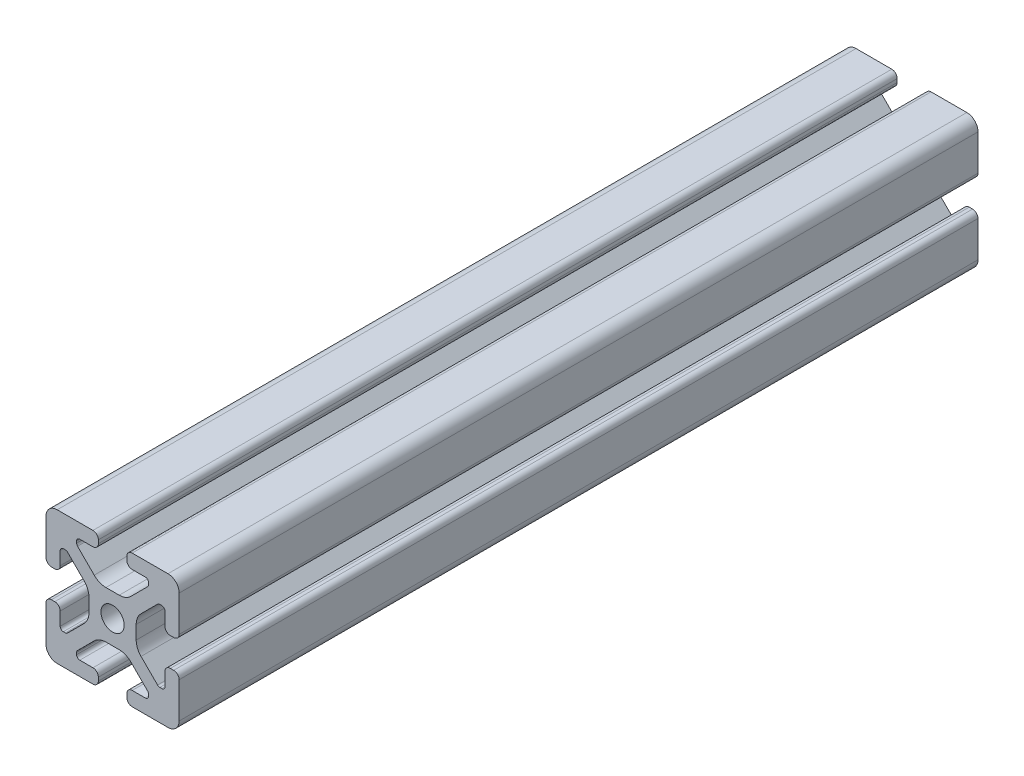
SolidWorks part; units mm, degrees
ref_plane "Front Plane" through (0, 0, 0) normal (0, 0, 1) x (1, 0, 0)
ref_plane "Top Plane" through (0, 0, 0) normal (0, 1, 0) x (1, 0, 0)
ref_plane "Right Plane" through (0, 0, 0) normal (1, 0, 0) x (0, 0, -1)
sketch "Sketch1" plane through (0, 0, 0) normal (0, 0, 1) x (1, 0, 0)
  point P0 (0, 0)
  line B0 (-4.064, 16.5396) -> (-4.064, 17.4964)
  line B1 (-5.6176, 19.05) -> (-15.8475, 19.05)
  line B2 (-19.05, 15.8475) -> (-19.05, 5.6176)
  line B3 (-17.4964, 4.064) -> (-16.5396, 4.064)
  line B4 (-14.986, 5.6176) -> (-14.986, 9.3853)
  line B5 (-14.0843, 10.287) -> (-13.516, 10.287)
  line B6 (-12.8784, 10.0229) -> (-8.1476, 5.2921)
  line B7 (-6.7564, 1.9335) -> (-6.7564, -1.9335)
  line B8 (-8.1476, -5.2921) -> (-12.8784, -10.0229)
  line B9 (-13.516, -10.287) -> (-14.0843, -10.287)
  line B10 (-14.986, -9.3853) -> (-14.986, -5.6176)
  line B11 (-16.5396, -4.064) -> (-17.4964, -4.064)
  line B12 (-19.05, -5.6176) -> (-19.05, -15.8475)
  line B13 (-15.8475, -19.05) -> (-5.6176, -19.05)
  line B14 (-4.064, -17.4964) -> (-4.064, -16.5396)
  line B15 (-5.6176, -14.986) -> (-9.3853, -14.986)
  line B16 (-10.287, -14.0843) -> (-10.287, -13.5524)
  line B17 (-10.0229, -12.9148) -> (-5.2522, -8.144)
  line B18 (-1.9022, -6.7564) -> (1.9022, -6.7564)
  line B19 (5.2522, -8.144) -> (10.0229, -12.9148)
  line B20 (10.287, -13.5524) -> (10.287, -14.0843)
  line B21 (9.3853, -14.986) -> (5.6176, -14.986)
  line B22 (4.064, -16.5396) -> (4.064, -17.4964)
  line B23 (5.6176, -19.05) -> (15.8475, -19.05)
  line B24 (19.05, -15.8475) -> (19.05, -5.6176)
  line B25 (17.4964, -4.064) -> (16.5396, -4.064)
  line B26 (14.986, -5.6176) -> (14.986, -9.3853)
  line B27 (14.0843, -10.287) -> (13.516, -10.287)
  line B28 (12.8784, -10.0229) -> (8.1476, -5.2921)
  line B29 (6.7564, -1.9335) -> (6.7564, 1.9335)
  line B30 (8.1476, 5.2921) -> (12.8784, 10.0229)
  line B31 (13.516, 10.287) -> (14.0843, 10.287)
  line B32 (14.986, 9.3853) -> (14.986, 5.6176)
  line B33 (16.5396, 4.064) -> (17.4964, 4.064)
  line B34 (19.05, 5.6176) -> (19.05, 15.8475)
  line B35 (15.8475, 19.05) -> (5.6176, 19.05)
  line B36 (4.064, 17.4964) -> (4.064, 16.5396)
  line B37 (5.6176, 14.986) -> (9.3853, 14.986)
  line B38 (10.287, 14.0843) -> (10.287, 13.5524)
  line B39 (10.0229, 12.9148) -> (5.2522, 8.144)
  line B40 (1.9022, 6.7564) -> (-1.9022, 6.7564)
  line B41 (-5.2522, 8.144) -> (-10.0229, 12.9148)
  line B42 (-10.287, 13.5524) -> (-10.287, 14.0843)
  line B43 (-9.3853, 14.986) -> (-5.6176, 14.986)
  arc B44 (-5.6176, 14.986) -> (-4.064, 16.5396) centre (-5.6176, 16.5396) ccw
  arc B45 (-4.064, 17.4964) -> (-5.6176, 19.05) centre (-5.6176, 17.4964) ccw
  arc B46 (-15.8475, 19.05) -> (-19.05, 15.8475) centre (-15.8751, 15.8751) ccw
  arc B47 (-19.05, 5.6176) -> (-17.4964, 4.064) centre (-17.4964, 5.6176) ccw
  arc B48 (-16.5396, 4.064) -> (-14.986, 5.6176) centre (-16.5396, 5.6176) ccw
  arc B49 (-14.0843, 10.287) -> (-14.986, 9.3853) centre (-14.0843, 9.3853) ccw
  arc B50 (-12.8784, 10.0229) -> (-13.516, 10.287) centre (-13.516, 9.3853) ccw
  arc B51 (-6.7564, 1.9335) -> (-8.1476, 5.2921) centre (-11.5062, 1.9335) ccw
  arc B52 (-8.1476, -5.2921) -> (-6.7564, -1.9335) centre (-11.5062, -1.9335) ccw
  arc B53 (-13.516, -10.287) -> (-12.8784, -10.0229) centre (-13.516, -9.3853) ccw
  arc B54 (-14.986, -9.3853) -> (-14.0843, -10.287) centre (-14.0843, -9.3853) ccw
  arc B55 (-14.986, -5.6176) -> (-16.5396, -4.064) centre (-16.5396, -5.6176) ccw
  arc B56 (-17.4964, -4.064) -> (-19.05, -5.6176) centre (-17.4964, -5.6176) ccw
  arc B57 (-19.05, -15.8475) -> (-15.8475, -19.05) centre (-15.8751, -15.8751) ccw
  arc B58 (-5.6176, -19.05) -> (-4.064, -17.4964) centre (-5.6176, -17.4964) ccw
  arc B59 (-4.064, -16.5396) -> (-5.6176, -14.986) centre (-5.6176, -16.5396) ccw
  arc B60 (-10.287, -14.0843) -> (-9.3853, -14.986) centre (-9.3853, -14.0843) ccw
  arc B61 (-10.0229, -12.9148) -> (-10.287, -13.5524) centre (-9.3853, -13.5524) ccw
  arc B62 (-1.9022, -6.7564) -> (-5.2522, -8.144) centre (-1.9022, -11.494) ccw
  arc B63 (5.2522, -8.144) -> (1.9022, -6.7564) centre (1.9022, -11.494) ccw
  arc B64 (10.287, -13.5524) -> (10.0229, -12.9148) centre (9.3853, -13.5524) ccw
  arc B65 (9.3853, -14.986) -> (10.287, -14.0843) centre (9.3853, -14.0843) ccw
  arc B66 (5.6176, -14.986) -> (4.064, -16.5396) centre (5.6176, -16.5396) ccw
  arc B67 (4.064, -17.4964) -> (5.6176, -19.05) centre (5.6176, -17.4964) ccw
  arc B68 (15.8475, -19.05) -> (19.05, -15.8475) centre (15.8751, -15.8751) ccw
  arc B69 (19.05, -5.6176) -> (17.4964, -4.064) centre (17.4964, -5.6176) ccw
  arc B70 (16.5396, -4.064) -> (14.986, -5.6176) centre (16.5396, -5.6176) ccw
  arc B71 (14.0843, -10.287) -> (14.986, -9.3853) centre (14.0843, -9.3853) ccw
  arc B72 (12.8784, -10.0229) -> (13.516, -10.287) centre (13.516, -9.3853) ccw
  arc B73 (6.7564, -1.9335) -> (8.1476, -5.2921) centre (11.5062, -1.9335) ccw
  arc B74 (8.1476, 5.2921) -> (6.7564, 1.9335) centre (11.5062, 1.9335) ccw
  arc B75 (13.516, 10.287) -> (12.8784, 10.0229) centre (13.516, 9.3853) ccw
  arc B76 (14.986, 9.3853) -> (14.0843, 10.287) centre (14.0843, 9.3853) ccw
  arc B77 (14.986, 5.6176) -> (16.5396, 4.064) centre (16.5396, 5.6176) ccw
  arc B78 (17.4964, 4.064) -> (19.05, 5.6176) centre (17.4964, 5.6176) ccw
  arc B79 (19.05, 15.8475) -> (15.8475, 19.05) centre (15.8751, 15.8751) ccw
  arc B80 (5.6176, 19.05) -> (4.064, 17.4964) centre (5.6176, 17.4964) ccw
  arc B81 (4.064, 16.5396) -> (5.6176, 14.986) centre (5.6176, 16.5396) ccw
  arc B82 (10.287, 14.0843) -> (9.3853, 14.986) centre (9.3853, 14.0843) ccw
  arc B83 (10.0229, 12.9148) -> (10.287, 13.5524) centre (9.3853, 13.5524) ccw
  arc B84 (1.9022, 6.7564) -> (5.2522, 8.144) centre (1.9022, 11.494) ccw
  arc B85 (-5.2522, 8.144) -> (-1.9022, 6.7564) centre (-1.9022, 11.494) ccw
  arc B86 (-10.287, 13.5524) -> (-10.0229, 12.9148) centre (-9.3853, 13.5524) ccw
  arc B87 (-9.3853, 14.986) -> (-10.287, 14.0843) centre (-9.3853, 14.0843) ccw
  circle B88 centre (0, 0) radius 3.3274
sketch_block_instance "Block-Sketch1-1"
sketch_block "Block-Sketch1"
sketch_block_instance "Block1-2"
sketch_block "Block1"
extrude "Boss-Extrude1" add sketch "Sketch1" along normal mid plane 228.6
